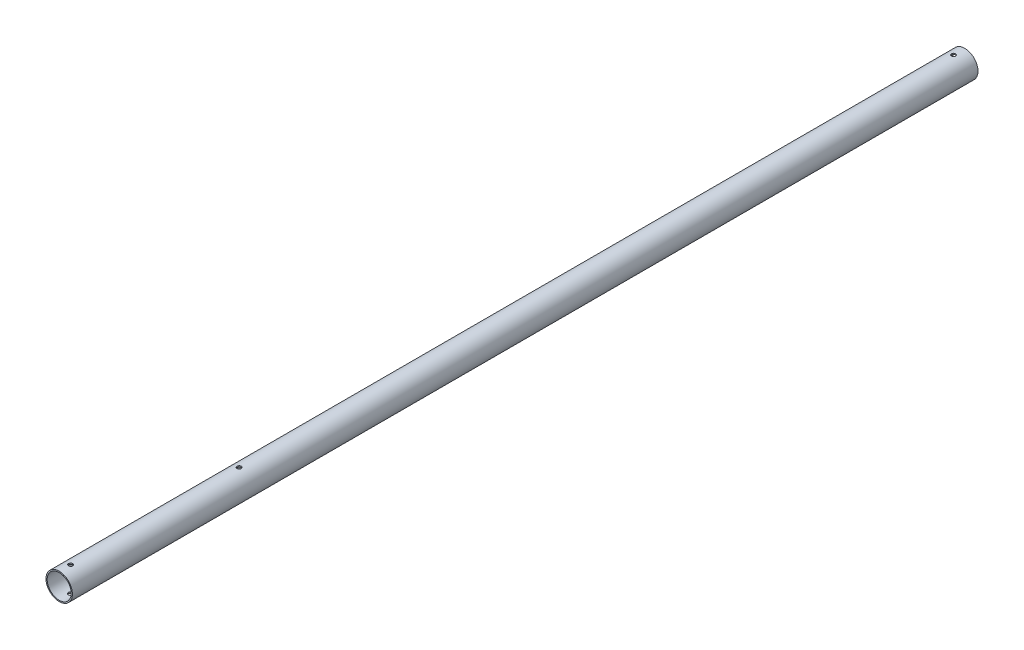
SolidWorks part; units mm, degrees
material "1060 Alloy"
ref_plane "Front Plane" through (0, 0, 0) normal (0, 0, 1) x (1, 0, 0)
ref_plane "Top Plane" through (0, 0, 0) normal (0, 1, 0) x (1, 0, 0)
ref_plane "Right Plane" through (0, 0, 0) normal (1, 0, 0) x (0, 0, -1)
sketch "Sketch2" plane through (0, 0, 0) normal (0, 0, 1) x (1, 0, 0)
  circle A0 centre (0, 0) radius 17.5
  circle A1 centre (0, 0) radius 15.9125
  dimension "D1" = 35
  dimension "D2" = 31.825
extrude "Boss-Extrude1" add sketch "Sketch2" along normal mid plane 1200
sketch "Sketch3" plane through (0, 0, 0) normal (0, 1, 0) x (1, 0, 0)
  line L0 (0, 600) -> (0, 585) construction
  line L1 (15.9125, 600) -> (-15.9125, 600) construction
  dimension "D1" = 15
hole_wizard "M5 Clearance Hole1" positions "Sketch4" profile "Sketch5" hole size "M5" standard "AS"
sketch "Sketch4" plane through (0, 0, 0) normal (0, 1, 0) x (1, 0, 0)
  point P0 (0, 585)
sketch "Sketch5" plane through (0, 0, -585) normal (1, 0, 0) x (0, 0, -1)
  line L0 (0, 0) -> (0, 17.5)
  line L1 (0, 17.5) -> (2.75, 17.5)
  line L2 (2.75, 17.5) -> (2.75, 0)
  line L5 (2.75, 0) -> (0, 0)
  line L11 (0, -6.35) -> (0, 107.95) construction
  dimension "Thru Hole Dia." = 5.5
  dimension "Thru Hole Depth" = 17.5
mirror "Mirror1" about plane through (0, 0, 0) normal (0, 1, 0) of "M5 Clearance Hole1"
mirror "Mirror2" about plane through (0, 0, 0) normal (0, 0, 1) of "Mirror1", "M5 Clearance Hole1"
sketch "Sketch6" plane through (0, 0, 0) normal (0, 1, 0) x (1, 0, 0)
  line L0 (0, -587.75) -> (0, -361.65) construction
  line L1 (-17.5, 600) -> (-17.5, -600) construction
  line L2 (19.0875, -570) -> (-19.0875, -570) construction
  circle A0 centre (0, -585) radius 2.75 construction
  circle A1 centre (0, -361.65) radius 2.75
  circle A2 centre (0, -585) radius 2.75 construction
  dimension "D1" = 208.35
extrude "Cut-Extrude1" cut sketch "Sketch6" against normal through all both and the other way through all
equation "\"frontTubeLength\"= 1200mm"
equation "\"D1@Boss-Extrude1\"=\"frontTubeLength\""
equation "\"outDiameter\"= 35mm"
equation "\"D1@Sketch2\"=\"outDiameter\""
equation "\"D2@Sketch2\"=\"outDiameter\"-0.125in"
